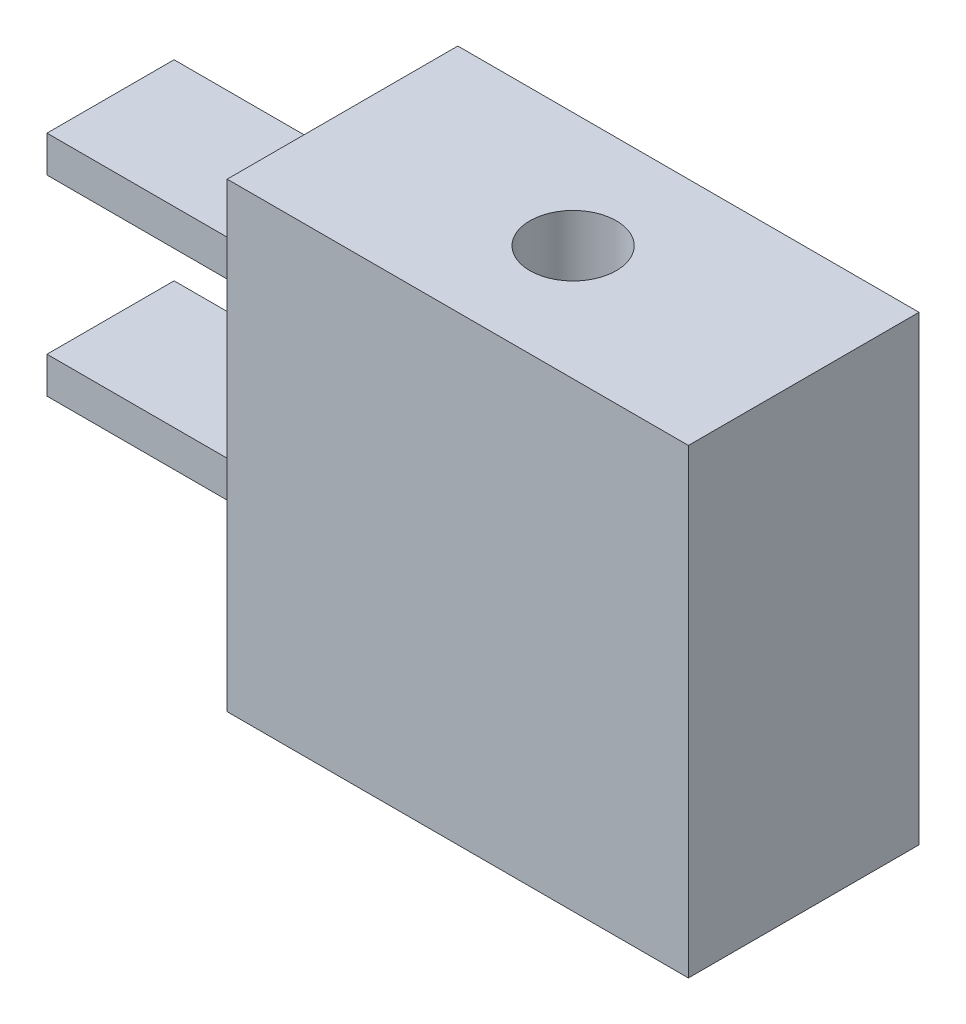
SolidWorks part; units mm, degrees
ref_plane "Front Plane" through (0, 0, 0) normal (0, 0, 1) x (1, 0, 0)
ref_plane "Top Plane" through (0, 0, 0) normal (0, 1, 0) x (1, 0, 0)
ref_plane "Right Plane" through (0, 0, 0) normal (1, 0, 0) x (0, 0, -1)
sketch "Sketch1" plane through (0, 0, 0) normal (0, 1, 0) x (1, 0, 0)
  line L1 (-6.35, -3.175) -> (6.35, -3.175)
  line L2 (-6.35, -3.175) -> (-6.35, 3.175)
  line L3 (-6.35, 3.175) -> (6.35, 3.175)
  line L4 (6.35, -3.175) -> (6.35, 3.175)
  line L5 (-6.35, -3.175) -> (6.35, 3.175) construction
  line L6 (-6.35, 3.175) -> (6.35, -3.175) construction
  point P0 (0, 0)
  dimension "D1" = 12.7
  dimension "D2" = 6.35
extrude "Boss-Extrude1" add sketch "Sketch1" along normal blind 12.7
sketch "Sketch2" plane through (0, 12.7, 0) normal (0, 1, 0) x (1, 0, 0)
  circle A0 centre (0, 0) radius 1.1906
  dimension "D1" = 2.3813
extrude "Cut-Extrude1" cut sketch "Sketch2" against normal blind 3
sketch "Sketch3" plane through (-6.35, 0, 0) normal (-1, 0, 0) x (0, 0, 1)
  line L1 (-1.7125, 3.6565) -> (1.7875, 3.6565)
  line L2 (-1.7125, 3.6565) -> (-1.7125, 4.6565)
  line L3 (-1.7125, 4.6565) -> (1.7875, 4.6565)
  line L4 (1.7875, 3.6565) -> (1.7875, 4.6565)
  line L5 (-1.7125, 3.6565) -> (1.7875, 4.6565) construction
  line L6 (-1.7125, 4.6565) -> (1.7875, 3.6565) construction
  line L7 (-1.7125, 8.9285) -> (1.7875, 8.9285)
  line L8 (-1.7125, 8.9285) -> (-1.7125, 9.9285)
  line L9 (-1.7125, 9.9285) -> (1.7875, 9.9285)
  line L10 (1.7875, 8.9285) -> (1.7875, 9.9285)
  line L11 (-1.7125, 8.9285) -> (1.7875, 9.9285) construction
  line L12 (-1.7125, 9.9285) -> (1.7875, 8.9285) construction
  point P0 (0.0375, 4.1565)
  point P5 (0.0375, 9.4285)
  dimension "D1" = 3.5
  dimension "D2" = 1
extrude "Boss-Extrude2" add sketch "Sketch3" along normal blind 6.35
